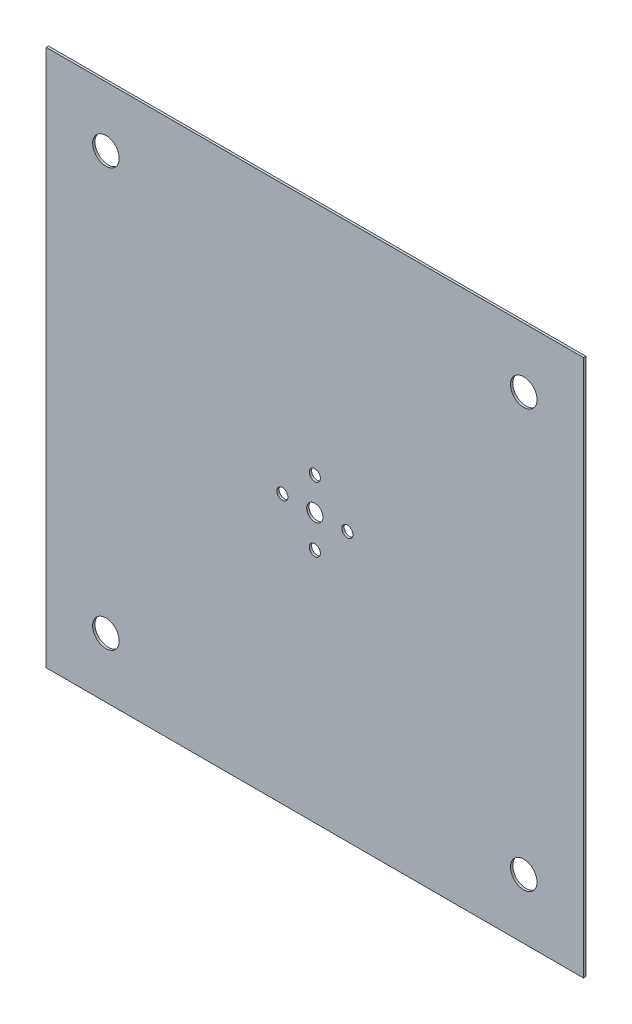
SolidWorks part; units mm, degrees
ref_plane "Front" through (0, 0, 0) normal (0, 0, 1) x (1, 0, 0)
ref_plane "Top" through (0, 0, 0) normal (0, 1, 0) x (1, 0, 0)
ref_plane "Right" through (0, 0, 0) normal (1, 0, 0) x (0, 0, -1)
sketch "Sketch1" plane through (0, 0, 0) normal (0, 0, 1) x (1, 0, 0)
  line L1 (-1157.4, 1157.4) -> (1157.4, 1157.4)
  line L2 (-1157.4, 1157.4) -> (-1157.4, -1157.4)
  line L3 (-1157.4, -1157.4) -> (1157.4, -1157.4)
  line L4 (1157.4, 1157.4) -> (1157.4, -1157.4)
  line L5 (-1157.4, 1157.4) -> (1157.4, -1157.4) construction
  line L6 (-1157.4, -1157.4) -> (1157.4, 1157.4) construction
  point P0 (0, 0)
  dimension "D1" = 2314.8
  dimension "D2" = 2314.8
extrude "Boss-Extrude1" add sketch "Sketch1" along normal blind 10
sketch "Sketch2" plane through (0, 0, 10) normal (0, 0, 1) x (1, 0, 0)
  line L0 (-1157.4, 0) -> (1157.4, 0) construction
  line L1 (-1157.4, 1157.4) -> (-1157.4, -1157.4) construction
  line L2 (1157.4, -1157.4) -> (1157.4, 1157.4) construction
  line L3 (0, 1157.4) -> (0, -1157.4) construction
  line L4 (1157.4, 1157.4) -> (-1157.4, 1157.4) construction
  line L5 (-1157.4, -1157.4) -> (1157.4, -1157.4) construction
  line L6 (0, 0) -> (-1157.4, 1157.4) construction
  circle A0 centre (0, 0) radius 35
  circle A1 centre (0, 140) radius 23.9
  circle A2 centre (0, -140) radius 23.9
  circle A3 centre (140, 0) radius 23.9
  circle A4 centre (-140, 0) radius 23.9
  circle A5 centre (-900, 900) radius 57.15
  circle A6 centre (900, 900) radius 57.15
  circle A7 centre (900, -900) radius 57.15
  circle A8 centre (-900, -900) radius 57.15
  dimension "D1" = 70
  dimension "D2" = 47.8
  dimension "D4" = 114.3
  dimension "D3" = 140
  dimension "D5" = 900
extrude "Cut-Extrude1" cut sketch "Sketch2" against normal blind 10
